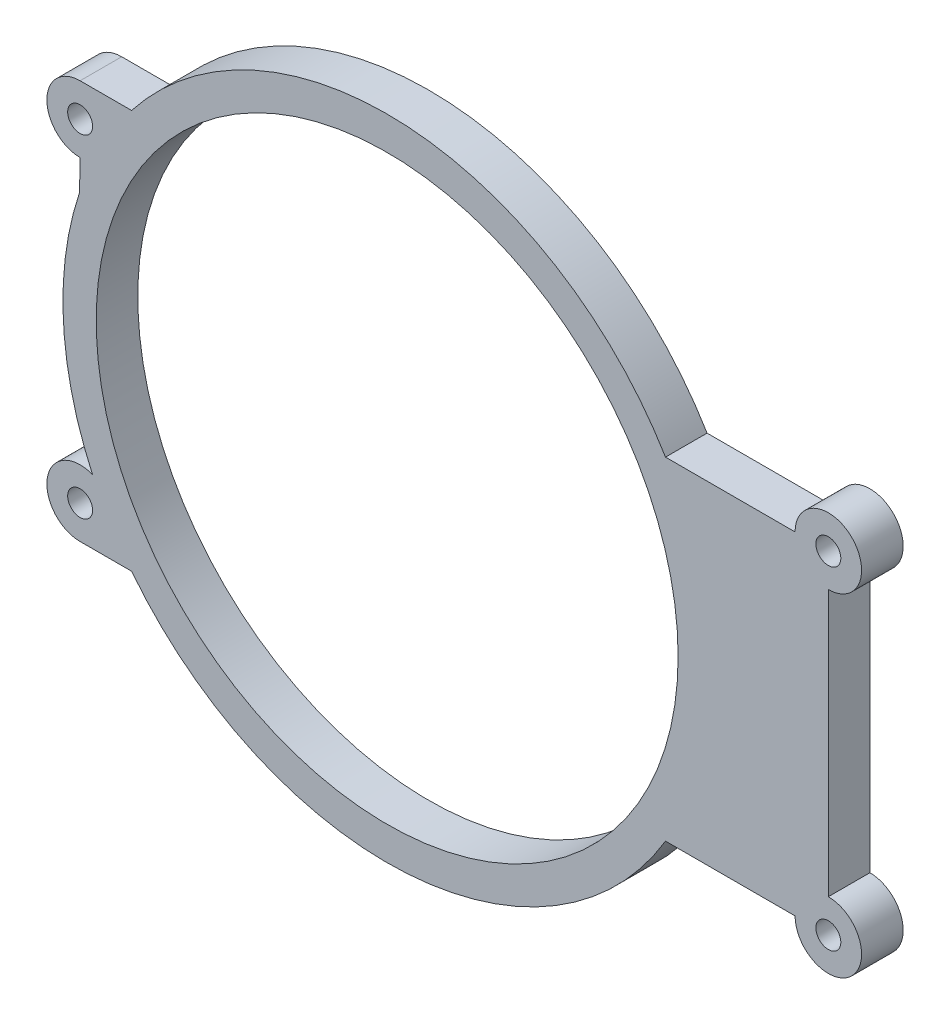
SolidWorks part; units mm, degrees
ref_plane "Front Plane" through (0, 0, 0) normal (0, 0, 1) x (1, 0, 0)
ref_plane "Top Plane" through (0, 0, 0) normal (0, 1, 0) x (1, 0, 0)
ref_plane "Right Plane" through (0, 0, 0) normal (1, 0, 0) x (0, 0, -1)
sketch "Sketch1" plane through (0, 0, 0) normal (0, 0, 1) x (1, 0, 0)
  line L0 (0, 0) -> (53.0676, 0) construction
  line L1 (53.0676, -20) -> (53.0676, 20)
  line L2 (0, 0) -> (-36.9324, 0) construction
  line L3 (-36.9324, -20) -> (-36.9324, 20) construction
  line L4 (49.0676, 20) -> (33.4813, 20)
  line L5 (0, 0) -> (-36.9324, 20) construction
  line L6 (49.0676, -20) -> (33.4813, -20)
  line L7 (-36.9324, 24) -> (-30.7409, 24)
  line L8 (-36.9324, 16) -> (-37.0028, 12.3203)
  line L9 (-36.9324, -24) -> (-30.7409, -24)
  line L10 (-36.9324, -16) -> (-36.9324, -12.53)
  circle A0 centre (0, 0) radius 35
  circle A1 centre (-36.9324, 20) radius 1.5
  circle A2 centre (53.0676, 20) radius 1.5
  circle A3 centre (53.0676, -20) radius 1.5
  circle A4 centre (-36.9324, -20) radius 1.5
  circle A5 centre (-36.9324, 20) radius 4
  circle A6 centre (-36.9324, -20) radius 4
  circle A7 centre (0, 0) radius 39
  circle A8 centre (53.0676, 20) radius 4
  circle A9 centre (53.0676, -20) radius 4
  point P7 (53.0676, 0)
  point P11 (-36.9324, 0)
  dimension "D1" = 70
  dimension "D6" = 3
  dimension "D7" = 3
  dimension "D8" = 3
  dimension "D9" = 3
  dimension "D10" = 8
  dimension "D11" = 78
  dimension "D12" = 8
  dimension "D13" = 8
  dimension "D14" = 8
  dimension "D2" = 90
  dimension "D3" = 40
  dimension "D4" = 40
  dimension "D5" = 42
extrude "Boss-Extrude1" add sketch "Sketch1" along normal blind 5
